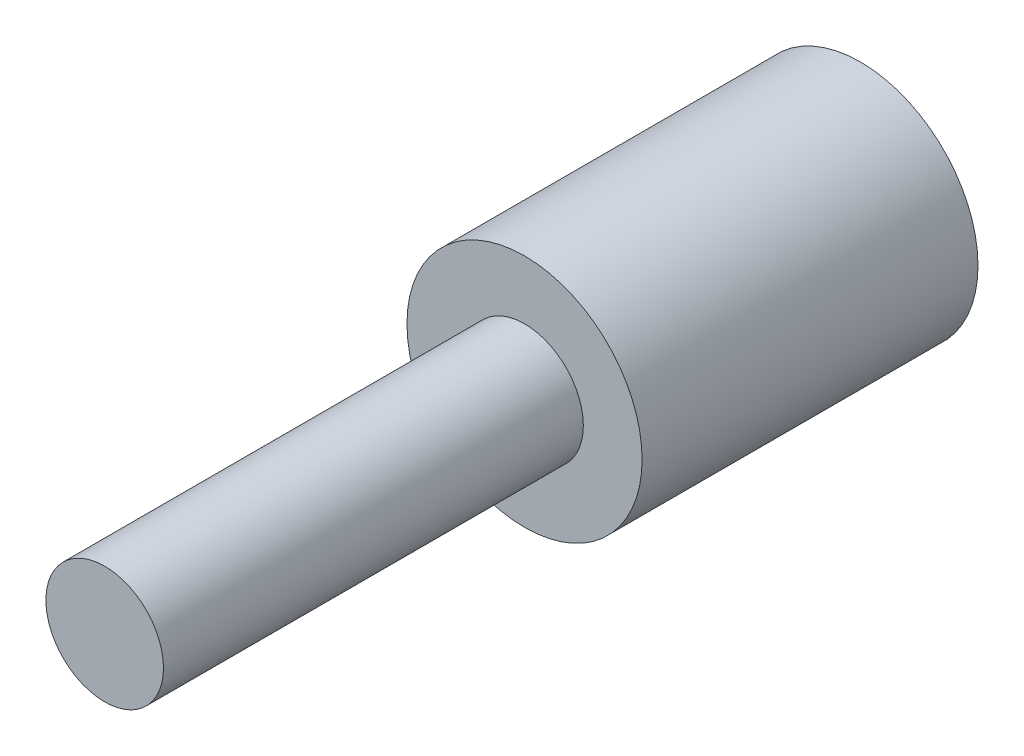
SolidWorks part; units mm, degrees
ref_plane "Front Plane" through (0, 0, 0) normal (0, 0, 1) x (1, 0, 0)
ref_plane "Top Plane" through (0, 0, 0) normal (0, 1, 0) x (1, 0, 0)
ref_plane "Right Plane" through (0, 0, 0) normal (1, 0, 0) x (0, 0, -1)
sketch "Sketch1" plane through (0, 0, 0) normal (0, 0, 1) x (1, 0, 0)
  circle A0 centre (0, 0) radius 2.2
  circle A1 centre (0, 0) radius 4.2
  dimension "D1" = 4.4
  dimension "D2" = 8.4
extrude "Boss-Extrude1" add sketch "Sketch1" along normal blind 10
sketch "Sketch2" plane through (0, 0, 10) normal (0, 0, 1) x (1, 0, 0)
  circle A0 centre (0, 0) radius 4.2
extrude "Boss-Extrude2" add sketch "Sketch2" along normal blind 2
sketch "Sketch3" plane through (0, 0, 12) normal (0, 0, 1) x (1, 0, 0)
  circle A0 centre (0, 0) radius 2.1
  dimension "D1" = 4.2
extrude "Boss-Extrude3" add sketch "Sketch3" along normal blind 15
